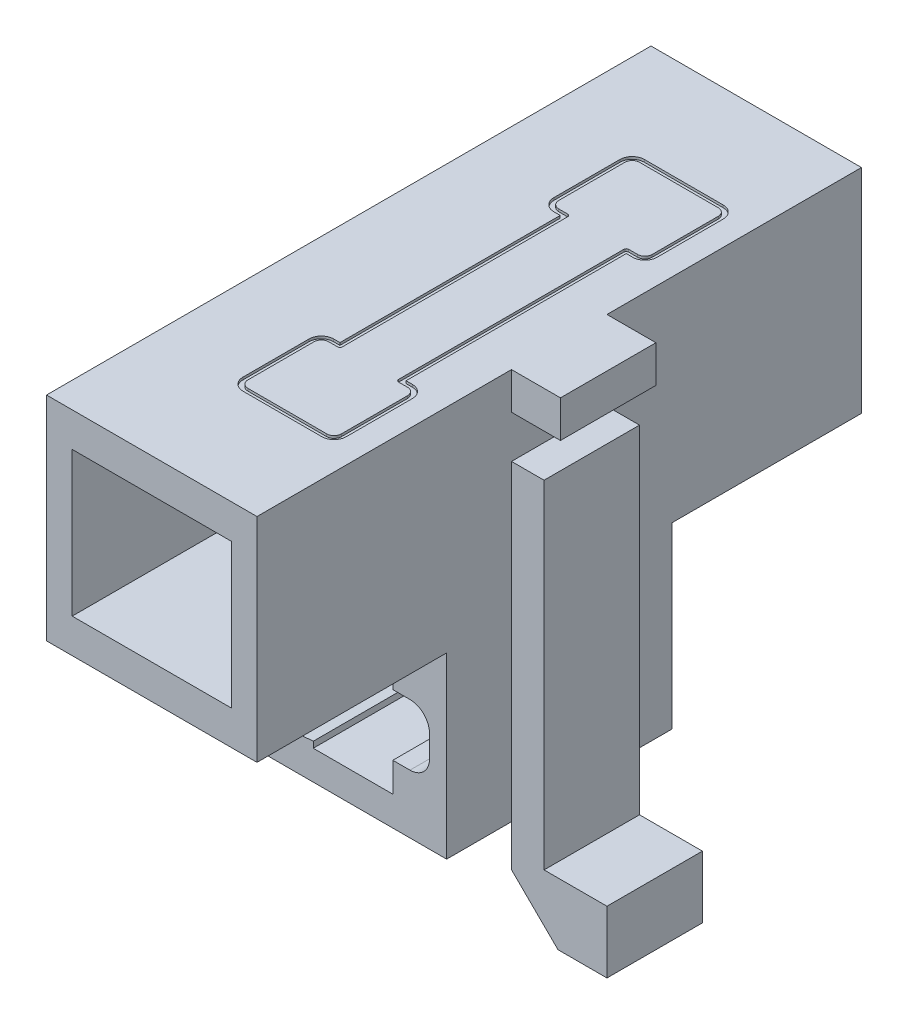
SolidWorks part; units mm, degrees
ref_plane "Front Plane" through (0, 0, 0) normal (0, 0, 1) x (1, 0, 0)
ref_plane "Top Plane" through (0, 0, 0) normal (0, 1, 0) x (1, 0, 0)
ref_plane "Right Plane" through (0, 0, 0) normal (1, 0, 0) x (0, 0, -1)
sketch "Sketch1" plane through (0, 0, 0) normal (0, 0, 1) x (1, 0, 0)
  line L1 (-4.3, 4.35) -> (4.3, 4.35)
  line L2 (-4.3, 4.35) -> (-4.3, -4.35)
  line L3 (-4.3, -4.35) -> (4.3, -4.35)
  line L4 (4.3, 4.35) -> (4.3, -4.35)
  line L5 (-3.25, 2.95) -> (3.25, 2.95)
  line L6 (-3.25, 2.95) -> (-3.25, -2.95)
  line L7 (-3.25, -2.95) -> (3.25, -2.95)
  line L8 (3.25, 2.95) -> (3.25, -2.95)
  dimension "D1" = 8.7
  dimension "D2" = 8.6
  dimension "D3" = 1.4
  dimension "D4" = 1.4
  dimension "D5" = 1.05
  dimension "D6" = 1.05
  dimension "D7" = 4.3
  dimension "D8" = 4.35
extrude "Boss-Extrude1" add sketch "Sketch1" along normal blind 24.7
ref_plane "Plane1" through (0, 0, 12.35) normal (0, 0, 1) x (1, 0, 0)
sketch "Sketch2" plane through (0, 0, 12.35) normal (0, 0, 1) x (1, 0, 0)
  line L0 (4.3, -4.35) -> (4.3, 4.35) construction
  line L1 (4.3, 4.35) -> (6.3, 4.35) construction
  line L2 (4.3, 4.35) -> (4.3, 2.84)
  line L3 (4.3, 2.84) -> (6.3, 2.84)
  line L4 (6.3, 4.35) -> (6.3, 2.84)
  line L5 (4.3, 1.1) -> (5.63, 1.1)
  line L6 (4.3, 1.1) -> (4.3, -13.35)
  line L8 (5.63, 1.1) -> (5.63, -12.69)
  line L9 (4.3, -13.35) -> (6.2, -15.23)
  line L10 (6.2, -15.23) -> (8.2, -15.23)
  line L12 (5.63, -12.69) -> (8.2, -12.69)
  line L13 (8.2, -15.23) -> (8.2, -12.69)
  line L14 (4.3, 4.35) -> (-4.3, 4.35) construction
  line L15 (-4.3, -4.35) -> (4.3, -4.35) construction
  line L16 (4.3, 4.35) -> (-4.3, 4.35) construction
  line L17 (4.3, 4.35) -> (6.3, 4.35)
  dimension "D1" = 1.51
  dimension "D2" = 1.33
  dimension "D3" = 3.9
  dimension "D4" = 2.54
  dimension "D5" = 19.58
  dimension "D6" = 2
  dimension "D7" = 9
  dimension "D8" = 3.25
  dimension "D9" = 2
extrude "Boss-Extrude2" add sketch "Sketch2" along normal blind 1.95 and the other way blind 1.95
sketch "Sketch3" plane through (0, 0, 12.35) normal (0, 0, 1) x (1, 0, 0)
  line L0 (4.3, -4.35) -> (4.3, -13.35) construction
  line L1 (-4.3, -4.35) -> (4.3, -4.35)
  line L2 (-4.3, -4.35) -> (-4.3, -11.65)
  line L3 (-4.3, -11.65) -> (4.3, -11.65)
  line L4 (4.3, -4.35) -> (4.3, -11.65)
  line L5 (4.3, 4.35) -> (-4.3, 4.35) construction
  line L6 (-4.3, -5.55) -> (-1.15, -5.8)
  line L7 (-1.15, -5.55) -> (2.1, -5.55)
  line L8 (-4.3, -5.55) -> (-4.3, -10.45)
  line L9 (-1.15, -10.45) -> (2.1, -10.45)
  line L10 (2.1, -5.55) -> (2.1, -6.75)
  line L11 (-1.15, -5.8) -> (-1.15, -5.55)
  line L12 (-4.3, -10.45) -> (-1.15, -10.2)
  line L13 (-1.15, -10.2) -> (-1.15, -10.45)
  line L14 (2.1, -9.25) -> (2.1, -10.45)
  line L15 (2.1, -6.75) -> (2.8, -6.75)
  line L17 (2.1, -9.25) -> (2.8, -9.25)
  line L18 (3.6, -7.55) -> (3.6, -8.45)
  arc A0 (2.8, -9.25) -> (3.6, -8.45) centre (2.8, -8.45) ccw
  arc A1 (2.8, -6.75) -> (3.6, -7.55) centre (2.8, -7.55) cw
  point P13 (-1.15, -10.325)
  point P24 (3.6, -9.25)
  point P27 (3.6, -6.75)
  dimension "D12" = 0.8
  dimension "D1" = 16
  dimension "D2" = 1.2
  dimension "D3" = 1.2
  dimension "D4" = 6.4
  dimension "D5" = 3.15
  dimension "D6" = 1.45
  dimension "D7" = 1.45
  dimension "D8" = 2.5
  dimension "D9" = 1.5
  dimension "D10" = 4.9
  dimension "D11" = 1.2
  dimension "D13" = 3.6
  dimension "D14" = 4.35
  dimension "D15" = 11.65
  dimension "D16" = 5.55
extrude "Boss-Extrude3" add sketch "Sketch3" along normal blind 4.6 and the other way blind 4.6 contours L15 A1 L18 A0 L17 L14 L9 L13 L12 L2 L3 L4 L1 L6 L11 L7 L10
sketch "Sketch4" plane through (0, 4.35, 0) normal (0, 1, 0) x (1, 0, 0)
  line L0 (-0.16, -12.35) -> (-0.16, -16.85)
  line L9 (-6.875, -12.35) -> (6.875, -12.35) construction
  line L10 (-0.16, -16.85) -> (-0.42, -16.85)
  line L11 (-0.42, -20.55) -> (2.8, -20.55)
  line L12 (2.8, -16.85) -> (2.54, -16.85)
  line L13 (2.54, -16.85) -> (2.54, -12.35)
  line L14 (-0.92, -20.05) -> (-0.92, -17.35)
  line L15 (3.3, -20.05) -> (3.3, -17.35)
  line L16 (4.3, -24.7) -> (4.3, -14.3) construction
  line L19 (4.3, 0) -> (-4.3, 0) construction
  line L20 (2.34, -16.95) -> (2.34, -7.75)
  line L21 (2.8, -17.05) -> (2.44, -17.05)
  line L22 (3.1, -20.05) -> (3.1, -17.35)
  line L23 (-0.42, -20.35) -> (2.8, -20.35)
  line L24 (-0.72, -20.05) -> (-0.72, -17.35)
  line L25 (-0.06, -17.05) -> (-0.42, -17.05)
  line L26 (0.04, -7.75) -> (0.04, -16.95)
  line L27 (2.34, -17.05) -> (2.34, -12.35) construction
  line L28 (2.8, -17.05) -> (2.34, -17.05) construction
  line L29 (0.04, -17.05) -> (-0.42, -17.05) construction
  line L30 (0.04, -12.35) -> (0.04, -17.05) construction
  line L31 (-5.2058, -12.35) -> (9.2224, -12.35) construction
  line L32 (-0.06, -7.65) -> (-0.42, -7.65)
  line L33 (-0.72, -4.65) -> (-0.72, -7.35)
  line L34 (-0.42, -4.35) -> (2.8, -4.35)
  line L35 (3.1, -4.65) -> (3.1, -7.35)
  line L36 (2.8, -7.65) -> (2.44, -7.65)
  line L37 (3.3, -4.65) -> (3.3, -7.35)
  line L38 (-0.92, -4.65) -> (-0.92, -7.35)
  line L39 (2.54, -7.85) -> (2.54, -12.35)
  line L40 (2.8, -7.85) -> (2.54, -7.85)
  line L41 (-0.42, -4.15) -> (2.8, -4.15)
  line L42 (-0.16, -7.85) -> (-0.42, -7.85)
  line L43 (-0.16, -12.35) -> (-0.16, -7.85)
  arc A0 (-0.42, -16.85) -> (-0.92, -17.35) centre (-0.42, -17.35) ccw
  arc A1 (3.3, -17.35) -> (2.8, -16.85) centre (2.8, -17.35) ccw
  arc A2 (2.8, -20.55) -> (3.3, -20.05) centre (2.8, -20.05) ccw
  arc A3 (-0.92, -20.05) -> (-0.42, -20.55) centre (-0.42, -20.05) ccw
  arc A4 (3.1, -17.35) -> (2.8, -17.05) centre (2.8, -17.35) ccw
  arc A5 (2.8, -20.35) -> (3.1, -20.05) centre (2.8, -20.05) ccw
  arc A6 (-0.72, -20.05) -> (-0.42, -20.35) centre (-0.42, -20.05) ccw
  arc A7 (-0.42, -17.05) -> (-0.72, -17.35) centre (-0.42, -17.35) ccw
  arc A8 (2.34, -16.95) -> (2.44, -17.05) centre (2.44, -16.95) ccw
  arc A9 (-0.06, -17.05) -> (0.04, -16.95) centre (-0.06, -16.95) ccw
  arc A10 (-0.06, -7.65) -> (0.04, -7.75) centre (-0.06, -7.75) cw
  arc A11 (2.34, -7.75) -> (2.44, -7.65) centre (2.44, -7.75) cw
  arc A12 (-0.42, -7.65) -> (-0.72, -7.35) centre (-0.42, -7.35) cw
  arc A13 (-0.72, -4.65) -> (-0.42, -4.35) centre (-0.42, -4.65) cw
  arc A14 (2.8, -4.35) -> (3.1, -4.65) centre (2.8, -4.65) cw
  arc A15 (3.1, -7.35) -> (2.8, -7.65) centre (2.8, -7.35) cw
  arc A16 (-0.92, -4.65) -> (-0.42, -4.15) centre (-0.42, -4.65) cw
  arc A17 (2.8, -4.15) -> (3.3, -4.65) centre (2.8, -4.65) cw
  arc A18 (3.3, -7.35) -> (2.8, -7.85) centre (2.8, -7.35) cw
  arc A19 (-0.42, -7.85) -> (-0.92, -7.35) centre (-0.42, -7.35) cw
  point P8 (-0.92, -4.15)
  point P17 (-0.92, -16.85)
  point P22 (3.3, -20.55)
  point P25 (-0.92, -20.55)
  point P70 (3.3, -4.15)
  point P84 (-0.92, -7.85)
  dimension "D9" = 0.5
  dimension "D11" = 0.1
  dimension "D1" = 4.22
  dimension "D2" = 2.7
  dimension "D3" = 3.7
  dimension "D4" = 0.76
  dimension "D5" = 1
  dimension "D6" = 0.76
  dimension "D7" = 8.2
  dimension "D8" = 16.85
  dimension "D10" = 0.2
extrude "Cut-Extrude1" cut sketch "Sketch4" against normal blind 0.1
equation "\"D7@Sketch1\"=\"D2@Sketch1\"/2"
equation "\"D8@Sketch1\"=\"D1@Sketch1\"/2"
equation "\"D11@Sketch3\"=(\"D10@Sketch3\"-\"D8@Sketch3\")/2"
equation "\"D4@Sketch4\"=(\"D1@Sketch4\"-\"D2@Sketch4\")/2"
